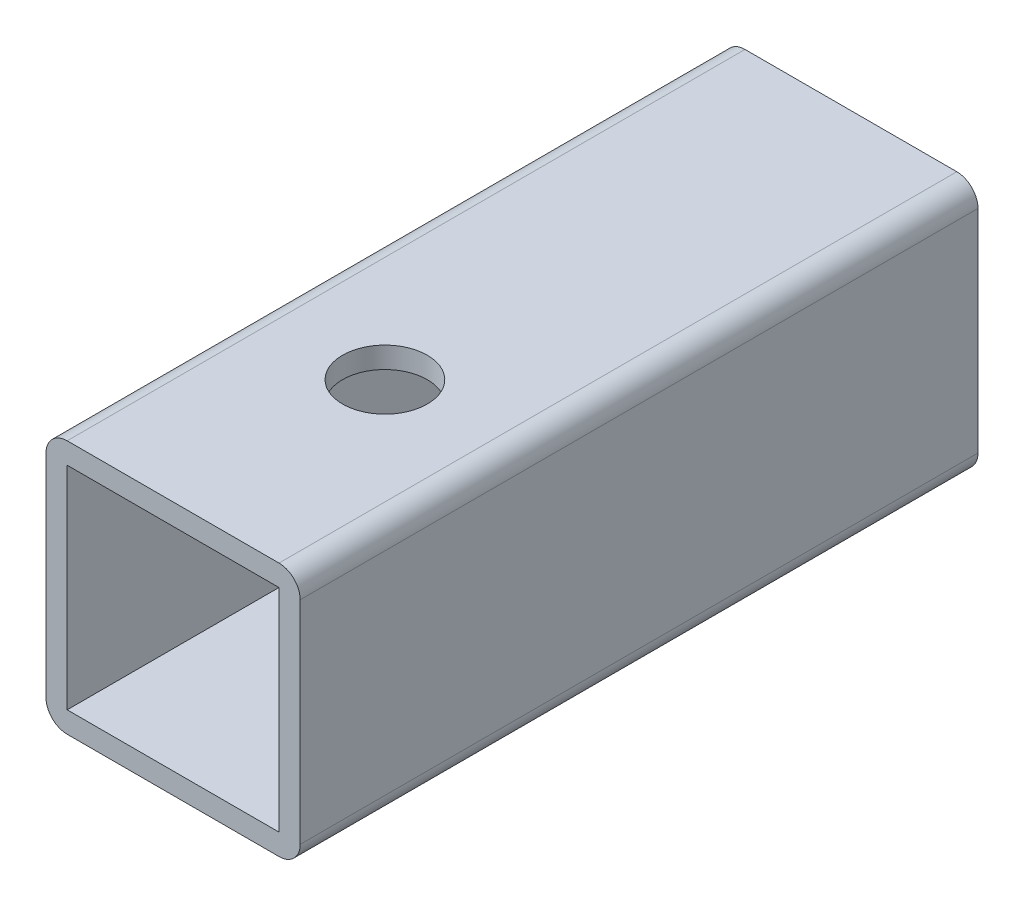
SolidWorks part; units mm, degrees
material "Plain Carbon Steel"
ref_plane "Front Plane" through (0, 0, 0) normal (0, 0, 1) x (1, 0, 0)
ref_plane "Top Plane" through (0, 0, 0) normal (0, 1, 0) x (1, 0, 0)
ref_plane "Right Plane" through (0, 0, 0) normal (1, 0, 0) x (0, 0, -1)
sketch "Sketch1" plane through (0, 0, 0) normal (0, 0, 1) x (1, 0, 0)
  line L1 (-19.05, -19.05) -> (19.05, -19.05)
  line L2 (-19.05, -19.05) -> (-19.05, 19.05)
  line L3 (-19.05, 19.05) -> (19.05, 19.05)
  line L4 (19.05, -19.05) -> (19.05, 19.05)
  line L5 (-19.05, -19.05) -> (19.05, 19.05) construction
  line L6 (-19.05, 19.05) -> (19.05, -19.05) construction
  line L7 (-15.875, -15.875) -> (15.875, -15.875)
  line L8 (-15.875, -15.875) -> (-15.875, 15.875)
  line L9 (-15.875, 15.875) -> (15.875, 15.875)
  line L10 (15.875, -15.875) -> (15.875, 15.875)
  line L11 (-15.875, -15.875) -> (15.875, 15.875) construction
  line L12 (-15.875, 15.875) -> (15.875, -15.875) construction
  point P0 (0, 0)
  point P6 (0, 0)
  dimension "D1" = 38.1
  dimension "D2" = 3.175
extrude "Extrude1" add sketch "Sketch1" along normal blind 101.6
fillet "Fillet1" radius 3.175 4 edges at (-19.05, 19.05, 50.8) (-19.05, -19.05, 50.8) (19.05, -19.05, 50.8) (19.05, 19.05, 50.8)
sketch "Sketch2" plane through (0, -19.05, 0) normal (0, -1, 0) x (1, 0, 0)
  line L0 (0, 101.6) -> (0, 69.85) construction
  line L2 (-15.875, 101.6) -> (15.875, 101.6) construction
  dimension "D1" = 31.75
hole_wizard "1/2 (0.5) Diameter Hole1" positions "Sketch4" profile "Sketch3" hole size "1/2" standard "Ansi Inch" end condition through all
sketch "Sketch4" plane through (0, -19.05, 0) normal (0, -1, 0) x (1, 0, 0)
  point P1 (0, 69.85)
sketch "Sketch3" plane through (0, -19.05, 69.85) normal (1, 0, 0) x (0, 0, -1)
  line L0 (0, 0) -> (0, 38.1)
  line L1 (0, 38.1) -> (6.35, 38.1)
  line L2 (6.35, 38.1) -> (6.35, 0)
  line L5 (6.35, 0) -> (0, 0)
  line L11 (0, -6.35) -> (0, 107.95) construction
  dimension "Thru Hole Dia." = 12.7
  dimension "Thru Hole Depth" = 38.1
